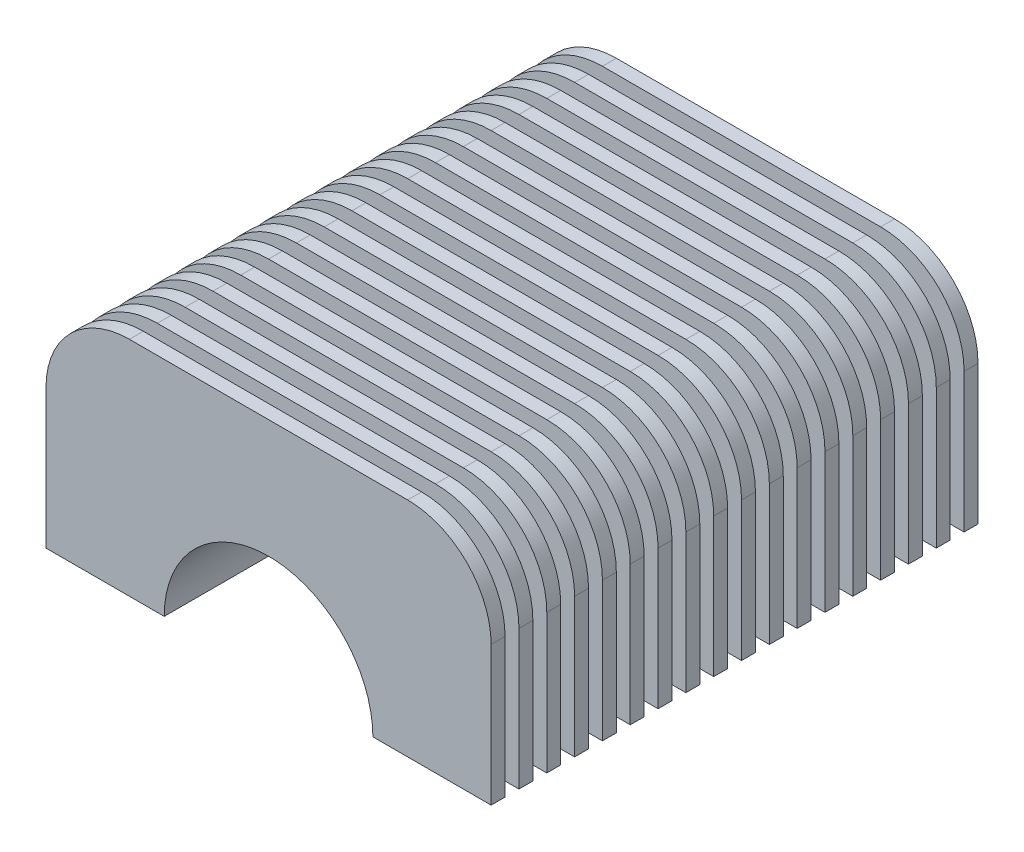
SolidWorks part; units mm, degrees
ref_plane "Front Plane" through (0, 0, 0) normal (0, 0, 1) x (1, 0, 0)
ref_plane "Top Plane" through (0, 0, 0) normal (0, 1, 0) x (1, 0, 0)
ref_plane "Right Plane" through (0, 0, 0) normal (1, 0, 0) x (0, 0, -1)
sketch "Sketch1" plane through (0, 0, 0) normal (0, 0, 1) x (1, 0, 0)
  line L0 (22.5, 0) -> (40, 0)
  line L1 (40, 0) -> (40, 40)
  line L2 (40, 40) -> (-40, 40)
  line L3 (-40, 40) -> (-40, 0)
  line L4 (-40, 0) -> (-22.5, 0)
  arc A0 (22.5, 0) -> (-22.5, 0) centre (0, 0) ccw
  point P9 (0, 0)
  dimension "D3" = 22.5
  dimension "D1" = 40
  dimension "D2" = 80
extrude "Boss-Extrude1" add sketch "Sketch1" along normal blind 108
fillet "Fillet1" radius 10 1 edges at (-40, 40, 54)
fillet "Fillet2" radius 10 1 edges at (40, 40, 54)
sketch "Sketch3" plane through (0, 0, 108) normal (0, 0, 1) x (1, 0, 0)
  line L0 (40, 0) -> (40, 30) construction
  line L1 (30, 40) -> (-30, 40) construction
  line L2 (-40, 30) -> (-40, 0) construction
  line L3 (40, 0) -> (40, 30)
  line L4 (30, 40) -> (-30, 40)
  line L5 (-40, 30) -> (-40, 0)
  line L6 (48, 0) -> (48, 30)
  line L7 (30, 48) -> (-30, 48)
  line L8 (-48, 30) -> (-48, 0)
  line L9 (-48, 0) -> (-40, 0)
  line L10 (40, 0) -> (48, 0)
  arc A0 (40, 30) -> (30, 40) centre (30, 30) ccw construction
  arc A1 (-30, 40) -> (-40, 30) centre (-30, 30) ccw construction
  arc A2 (40, 30) -> (30, 40) centre (30, 30) ccw
  arc A3 (-30, 40) -> (-40, 30) centre (-30, 30) ccw
  arc A4 (48, 30) -> (30, 48) centre (30, 30) ccw
  arc A5 (-30, 48) -> (-48, 30) centre (-30, 30) ccw
  dimension "D1" = 8
extrude "Boss-Extrude3" add sketch "Sketch3" against normal blind 3
pattern_linear "LPattern1" count 18 spacing 6 along (0, 0, -1) of "Boss-Extrude3"
